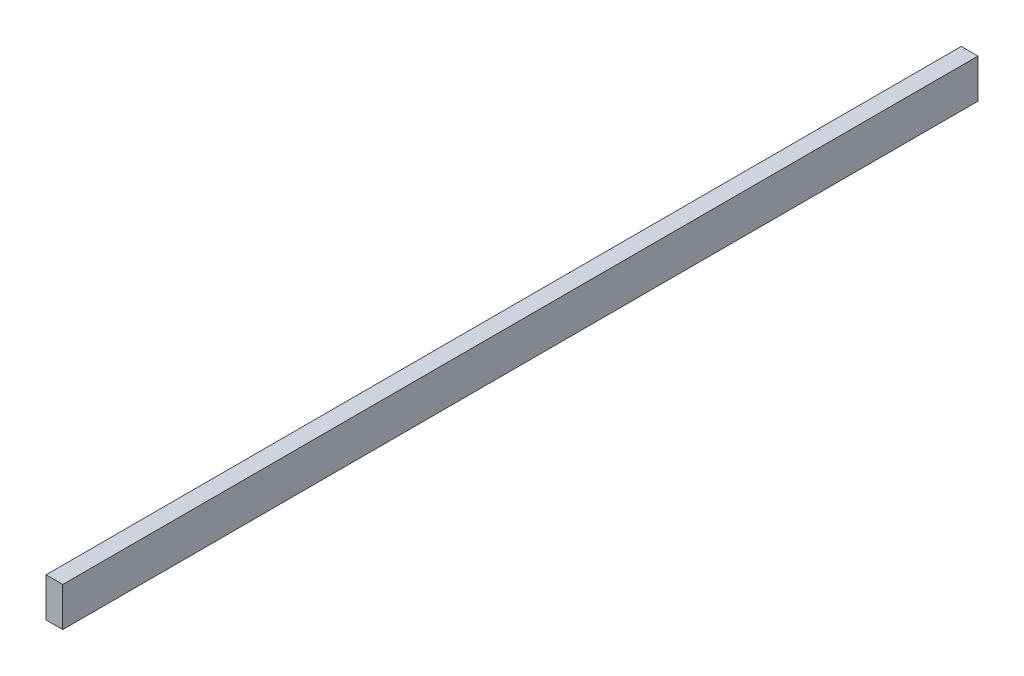
SolidWorks part; units mm, degrees
ref_plane "Front Plane" through (0, 0, 0) normal (0, 0, 1) x (1, 0, 0)
ref_plane "Top Plane" through (0, 0, 0) normal (0, 1, 0) x (1, 0, 0)
ref_plane "Right Plane" through (0, 0, 0) normal (1, 0, 0) x (0, 0, -1)
sketch "Sketch1" plane through (0, 0, 0) normal (1, 0, 0) x (0, 0, -1)
  line L1 (-1041.4, 44.45) -> (1041.4, 44.45)
  line L2 (-1041.4, 44.45) -> (-1041.4, -44.45)
  line L3 (-1041.4, -44.45) -> (1041.4, -44.45)
  line L4 (1041.4, 44.45) -> (1041.4, -44.45)
  line L5 (-1041.4, 44.45) -> (1041.4, -44.45) construction
  line L6 (-1041.4, -44.45) -> (1041.4, 44.45) construction
  point P0 (0, 0)
  dimension "D1" = 88.9
  dimension "D2" = 2082.8
extrude "Boss-Extrude1" add sketch "Sketch1" along normal blind 38.1
sketch "Sketch2" [suppressed] plane through (38.1, 0, 0) normal (1, 0, 0) x (0, 0, -1)
  line L0 (1041.4, 44.45) -> (-1041.4, 44.45) construction
  line L1 (-50.8, 44.45) -> (406.4, 44.45)
  line L2 (-50.8, 44.45) -> (-50.8, -44.45)
  line L3 (-50.8, -44.45) -> (406.4, -44.45)
  line L4 (406.4, 44.45) -> (406.4, -44.45)
  line L5 (-1041.4, -44.45) -> (1041.4, -44.45) construction
  line L6 (-1041.4, 44.45) -> (-1041.4, -44.45) construction
  line L7 (1041.4, -44.45) -> (1041.4, 44.45) construction
  dimension "D1" = 990.6
  dimension "D2" = 635
extrude "Cut-Extrude1" [suppressed] cut sketch "Sketch2" against normal through all contours L2 L3 L4 L1
